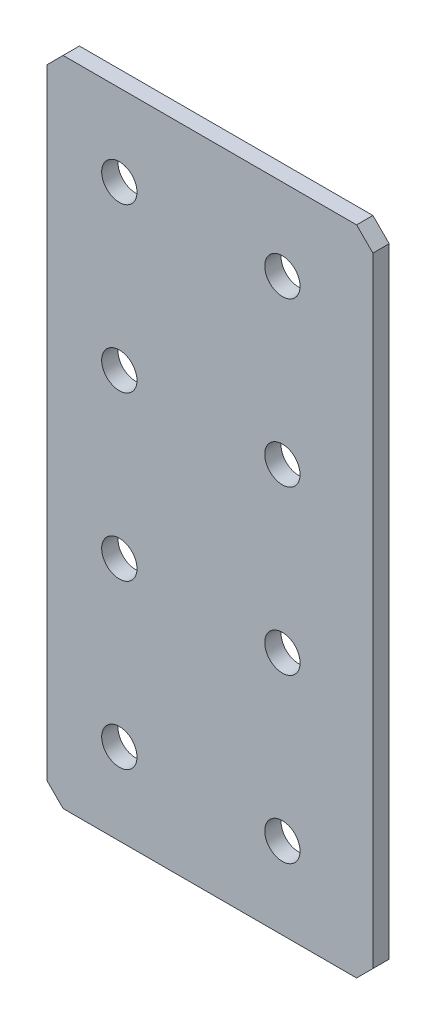
SolidWorks part; units mm, degrees
ref_plane "Front Plane" through (0, 0, 0) normal (0, 0, 1) x (1, 0, 0)
ref_plane "Top Plane" through (0, 0, 0) normal (0, 1, 0) x (1, 0, 0)
ref_plane "Right Plane" through (0, 0, 0) normal (1, 0, 0) x (0, 0, -1)
sketch "Sketch1" plane through (0, 0, 0) normal (0, 0, 1) x (1, 0, 0)
  line L1 (-17.6271, 51.8435) -> (42.3729, 51.8435)
  line L2 (-17.6271, 51.8435) -> (-17.6271, -68.1565)
  line L3 (-17.6271, -68.1565) -> (42.3729, -68.1565)
  line L4 (42.3729, 51.8435) -> (42.3729, -68.1565)
  circle A0 centre (-4.282, 36.8435) radius 3.25
  circle A1 centre (25.718, 36.8435) radius 3.25
  circle A2 centre (-4.282, 6.8435) radius 3.25
  circle A3 centre (25.718, 6.8435) radius 3.25
  circle A4 centre (-4.282, -23.1565) radius 3.25
  circle A5 centre (25.718, -23.1565) radius 3.25
  circle A6 centre (-4.282, -53.1565) radius 3.25
  circle A7 centre (25.718, -53.1565) radius 3.25
  point P20 (0, 0)
  point P21 (0, 0)
  point P22 (0, 0)
  point P23 (0, 0)
  point P24 (0, 0)
  point P25 (0, 0)
  point P26 (0, 0)
  point P27 (0, 0)
  point P28 (0, 0)
  point P29 (0, 0)
  point P31 (-4.0362, -54.1482)
  point P32 (-5.4051, 6.0863)
  dimension "D3" = 6.5
  dimension "D7" = 30
  dimension "D8" = 30
  dimension "D1" = 60
  dimension "D2" = 120
  dimension "D4" = 30
  dimension "D5" = 15
  dimension "D6" = 60
extrude "Boss-Extrude1" add sketch "Sketch1" along normal blind 3
chamfer "Chamfer1" distance 3 angle 45 4 edges at (-17.6271, -68.1565, 1.5) (42.3729, -68.1565, 1.5) (42.3729, 51.8435, 1.5) (-17.6271, 51.8435, 1.5)
